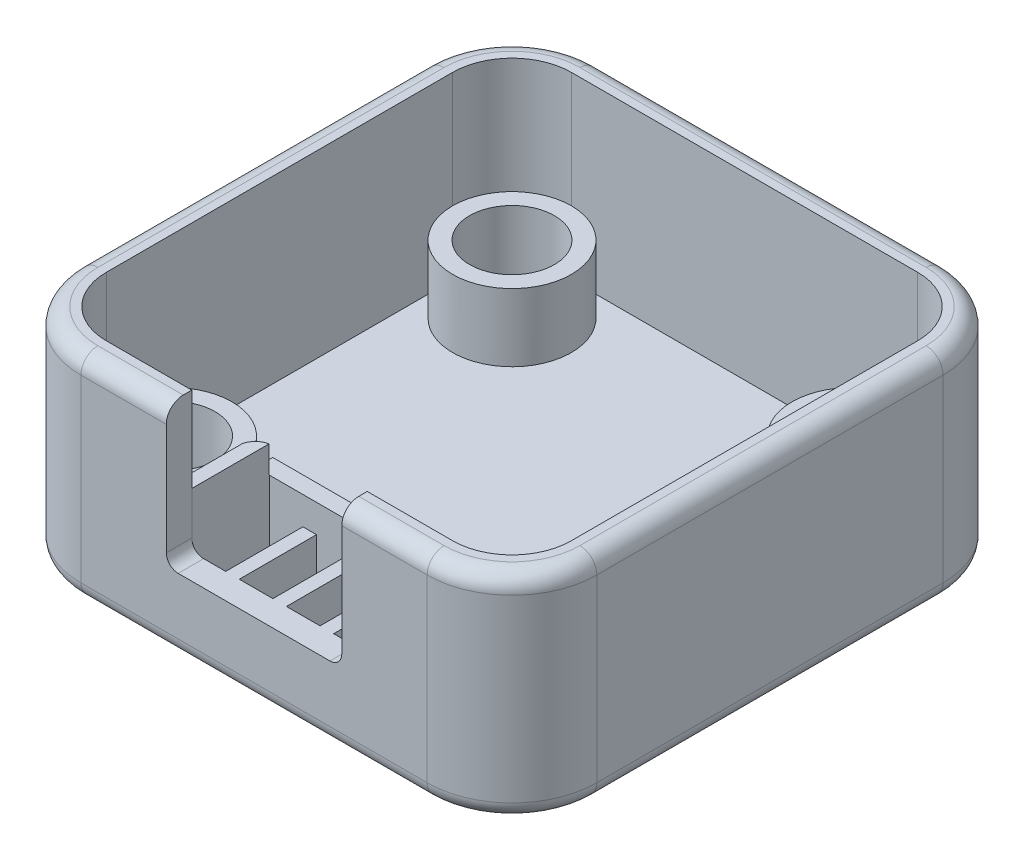
SolidWorks part; units mm, degrees
ref_plane "Front Plane" through (0, 0, 0) normal (0, 0, 1) x (1, 0, 0)
ref_plane "Top Plane" through (0, 0, 0) normal (0, 1, 0) x (1, 0, 0)
ref_plane "Right Plane" through (0, 0, 0) normal (1, 0, 0) x (0, 0, -1)
sketch "Sketch2" plane through (0, -1.6, 0) normal (0, -1, 0) x (1, 0, 0)
  line L1 (-13.5, -3.5) -> (-13.5, -23.5) construction
  line L2 (15.2, -28.7) -> (-15.2, -28.7)
  line L3 (15.2, -28.7) -> (15.2, 1.7)
  line L4 (15.2, 1.7) -> (-15.2, 1.7)
  line L5 (-15.2, -28.7) -> (-15.2, 1.7)
  line L6 (-6.77, 0) -> (-10, 0) construction
  line L7 (13.5, -23.5) -> (13.5, -3.5) construction
  line L8 (9, -27) -> (-9, -27) construction
  dimension "D1" = 1.7
  dimension "D2" = 1.7
  dimension "D3" = 1.7
  dimension "D4" = 1.7
extrude "Boss-Extrude1" add sketch "Sketch2" along normal blind 6
fillet "Fillet1" radius 5 4 edges at (15.2, -4.6, 1.7) (15.2, -4.6, -28.7) (-15.2, -4.6, 1.7) (-15.2, -4.6, -28.7)
fillet "Fillet2" radius 1 8 edges at (13.7355, -7.6, -27.2355) (15.2, -7.6, -13.5) (13.7355, -7.6, 0.2355) (0, -7.6, 1.7) (-13.7355, -7.6, 0.2355) (-15.2, -7.6, -13.5) (-13.7355, -7.6, -27.2355) (0, -7.6, -28.7)
sketch "Sketch3" plane through (0, -7.6, 0) normal (0, -1, 0) x (1, 0, 0)
  line L12 (10.2, -1.8) -> (-10.2, -1.8)
  line L13 (11.7, -23.7) -> (11.7, -3.3)
  line L14 (-10.2, -25.2) -> (10.2, -25.2)
  line L15 (-11.7, -3.3) -> (-11.7, -23.7)
  line L16 (10.2, -1.8) -> (-10.2, -1.8)
  line L17 (11.7, -23.7) -> (11.7, -3.3)
  line L18 (-10.2, -25.2) -> (10.2, -25.2)
  line L19 (-11.7, -3.3) -> (-11.7, -23.7)
  arc A12 (-10.2, -1.8) -> (-11.7, -3.3) centre (-10.2, -3.3) ccw
  arc A13 (11.7, -3.3) -> (10.2, -1.8) centre (10.2, -3.3) ccw
  arc A14 (10.2, -25.2) -> (11.7, -23.7) centre (10.2, -23.7) ccw
  arc A15 (-11.7, -23.7) -> (-10.2, -25.2) centre (-10.2, -23.7) ccw
  arc A16 (-10.2, -1.8) -> (-11.7, -3.3) centre (-10.2, -3.3) ccw
  arc A17 (11.7, -3.3) -> (10.2, -1.8) centre (10.2, -3.3) ccw
  arc A18 (10.2, -25.2) -> (11.7, -23.7) centre (10.2, -23.7) ccw
  arc A19 (-11.7, -23.7) -> (-10.2, -25.2) centre (-10.2, -23.7) ccw
  dimension "D1" = 3.5
extrude "Cut-Extrude1" cut sketch "Sketch3" against normal blind 0.5
sketch "Sketch4" plane through (0, -1.6, 0) normal (0, 1, 0) x (1, 0, 0)
  line L0 (15.2, 23.7) -> (15.2, 3.3) construction
  line L1 (-10.2, 28.7) -> (10.2, 28.7) construction
  line L2 (-15.2, 3.3) -> (-15.2, 23.7) construction
  line L3 (10.2, -1.7) -> (-10.2, -1.7) construction
  line L4 (15.2, 23.7) -> (15.2, 3.3)
  line L5 (-10.2, 28.7) -> (10.2, 28.7)
  line L6 (-15.2, 3.3) -> (-15.2, 23.7)
  line L7 (10.2, -1.7) -> (-10.2, -1.7)
  arc A0 (15.2, 23.7) -> (10.2, 28.7) centre (10.2, 23.7) ccw construction
  arc A1 (-10.2, 28.7) -> (-15.2, 23.7) centre (-10.2, 23.7) ccw construction
  arc A2 (-15.2, 3.3) -> (-10.2, -1.7) centre (-10.2, 3.3) ccw construction
  arc A3 (10.2, -1.7) -> (15.2, 3.3) centre (10.2, 3.3) ccw construction
  arc A4 (15.2, 23.7) -> (10.2, 28.7) centre (10.2, 23.7) ccw
  arc A5 (-10.2, 28.7) -> (-15.2, 23.7) centre (-10.2, 23.7) ccw
  arc A6 (-15.2, 3.3) -> (-10.2, -1.7) centre (-10.2, 3.3) ccw
  arc A7 (10.2, -1.7) -> (15.2, 3.3) centre (10.2, 3.3) ccw
extrude "Boss-Extrude2" add sketch "Sketch4" along normal blind 6.6
sketch "Sketch5" plane through (0, 5, 0) normal (0, 1, 0) x (1, 0, 0)
  line L8 (10.2, 27.2) -> (-10.2, 27.2)
  line L9 (-13.7, 23.7) -> (-13.7, 3.3)
  line L10 (-10.2, -0.2) -> (10.2, -0.2)
  line L11 (13.7, 3.3) -> (13.7, 23.7)
  line L12 (10.2, 27.2) -> (-10.2, 27.2)
  line L13 (-13.7, 23.7) -> (-13.7, 3.3)
  line L14 (-10.2, -0.2) -> (10.2, -0.2)
  line L15 (13.7, 3.3) -> (13.7, 23.7)
  arc A8 (13.7, 23.7) -> (10.2, 27.2) centre (10.2, 23.7) ccw
  arc A9 (-10.2, 27.2) -> (-13.7, 23.7) centre (-10.2, 23.7) ccw
  arc A10 (-13.7, 3.3) -> (-10.2, -0.2) centre (-10.2, 3.3) ccw
  arc A11 (10.2, -0.2) -> (13.7, 3.3) centre (10.2, 3.3) ccw
  arc A12 (13.7, 23.7) -> (10.2, 27.2) centre (10.2, 23.7) ccw
  arc A13 (-10.2, 27.2) -> (-13.7, 23.7) centre (-10.2, 23.7) ccw
  arc A14 (-13.7, 3.3) -> (-10.2, -0.2) centre (-10.2, 3.3) ccw
  arc A15 (10.2, -0.2) -> (13.7, 3.3) centre (10.2, 3.3) ccw
  dimension "D1" = 1.5
extrude "Cut-Extrude2" cut sketch "Sketch5" against normal offset from surface (10.6 mm away) 1.5 up to face at (0, -7.1, -13.5)
fillet "Fillet3" radius 1 8 edges at (13.7355, 5, -27.2355) (0, 5, -28.7) (-13.7355, 5, -27.2355) (-15.2, 5, -13.5) (-13.7355, 5, 0.2355) (0, 5, 1.7) (13.7355, 5, 0.2355) (15.2, 5, -13.5)
sketch "Sketch6" plane through (0, 0, 1.7) normal (0, 0, 1) x (1, 0, 0)
  line L0 (5.17, -2.55) -> (5.17, 0.95) construction
  line L2 (-5.17, 0.95) -> (-5.17, -2.55) construction
  line L3 (-4.47, -3.25) -> (4.47, -3.25) construction
  line L4 (5.17, -2.55) -> (5.17, 5)
  line L6 (-5.17, 5) -> (-5.17, -2.55)
  line L7 (-4.47, -3.25) -> (4.47, -3.25)
  line L8 (-10.2, 5) -> (10.2, 5) construction
  line L9 (-5.17, 5) -> (5.17, 5)
  arc A0 (4.47, -3.25) -> (5.17, -2.55) centre (4.47, -2.55) ccw construction
  arc A3 (-5.17, -2.55) -> (-4.47, -3.25) centre (-4.47, -2.55) ccw construction
  arc A4 (4.47, -3.25) -> (5.17, -2.55) centre (4.47, -2.55) ccw
  arc A7 (-5.17, -2.55) -> (-4.47, -3.25) centre (-4.47, -2.55) ccw
extrude "Cut-Extrude3" cut sketch "Sketch6" against normal up to next
sketch "Sketch9" plane through (0, -5.6, 0) normal (0, 1, 0) x (1, 0, 0)
  line L0 (5.97, 3.35) -> (5.97, 0) construction
  line L1 (5.17, 4.35) -> (5.17, 0) construction
  line L2 (5.97, 5.35) -> (5.97, -0.2)
  line L3 (5.17, 5.35) -> (5.17, -0.2)
  line L5 (5.97, -0.2) -> (5.17, -0.2)
  line L6 (5.17, 5.35) -> (5.97, 5.35)
  line L7 (5.17, -0.2) -> (10.2, -0.2) construction
  point P11 (5.57, -0.2)
extrude "Boss-Extrude5" add sketch "Sketch9" along normal up to vertex (2.35 mm away)
pattern_linear "LPattern1" count 5 spacing 2.78 along (-1, 0, 0) of "Boss-Extrude5"
sketch "Sketch10" plane through (0, 0, -5.35) normal (0, 0, -1) x (-1, 0, 0)
  line L0 (5.95, -3.25) -> (5.95, -5.6) construction
  line L1 (-5.97, -3.25) -> (-5.97, -5.6) construction
  line L2 (5.95, -3.25) -> (5.95, -5.6)
  line L3 (-5.97, -3.25) -> (-5.97, -5.6)
  line L4 (-5.97, -5.6) -> (5.95, -5.6)
  line L5 (5.95, -3.25) -> (-5.97, -3.25)
extrude "Boss-Extrude6" add sketch "Sketch10" against normal blind 1
sketch "Sketch11" plane through (0, -3.25, 0) normal (0, 1, 0) x (1, 0, 0)
  line L0 (3.19, 4.35) -> (5.17, 4.35) construction
  line L1 (5.17, -0.2) -> (5.97, -0.2) construction
  line L2 (5.17, 4.35) -> (5.17, -0.2) construction
  line L3 (-5.15, -0.2) -> (-5.15, 4.35) construction
  line L4 (-5.95, -0.2) -> (-5.15, -0.2) construction
  line L5 (-5.95, 5.35) -> (-5.95, -0.2) construction
  line L6 (5.97, 5.35) -> (-5.95, 5.35) construction
  line L7 (5.97, -0.2) -> (5.97, 5.35) construction
  line L8 (-5.15, 4.35) -> (5.17, 4.35)
  line L9 (5.17, -0.2) -> (5.97, -0.2)
  line L10 (5.17, 4.35) -> (5.17, -0.2)
  line L11 (-5.15, -0.2) -> (-5.15, 4.35)
  line L12 (-5.95, -0.2) -> (-5.15, -0.2)
  line L13 (-5.95, 5.35) -> (-5.95, -0.2)
  line L14 (5.97, 5.35) -> (-5.95, 5.35)
  line L15 (5.97, -0.2) -> (5.97, 5.35)
extrude "Boss-Extrude7" add sketch "Sketch11" along normal up to vertex (1.65 mm away)
sketch "Sketch12" plane through (0, -5.6, 0) normal (0, 1, 0) x (1, 0, 0)
  circle A0 centre (10, 3.5) radius 3.5
  circle A1 centre (10, 23.5) radius 3.5
  circle A2 centre (-10, 23.5) radius 3.5
  circle A3 centre (-10, 3.5) radius 3.5
  circle A4 centre (10, 23.5) radius 2.5
  circle A5 centre (-10, 23.5) radius 2.5
  circle A6 centre (10, 3.5) radius 2.5
  circle A7 centre (-10, 3.5) radius 2.5
  dimension "D1" = 7
  dimension "D2" = 5
extrude "Boss-Extrude8" add sketch "Sketch12" along normal up to vertex (3.99 mm away)
sketch "Sketch13" plane through (0, -1.6, 0) normal (0, 1, 0) x (1, 0, 0)
  line L0 (-5.95, -0.2) -> (-5.17, -0.2) construction
  line L1 (-5.15, -0.2) -> (-5.15, 4.35) construction
  line L2 (-5.95, 5.35) -> (-5.95, -0.2) construction
  line L3 (-5.95, -0.2) -> (-5.15, -0.2)
  line L4 (-5.15, -0.2) -> (-5.15, 4.3337)
  line L5 (-5.95, 3.549) -> (-5.95, -0.2)
  line L6 (5.17, -0.2) -> (5.97, -0.2) construction
  line L7 (5.17, 4.35) -> (5.17, -0.2) construction
  line L8 (5.97, -0.2) -> (5.97, 5.35) construction
  line L9 (5.17, -0.2) -> (5.97, -0.2)
  line L10 (5.17, 4.3298) -> (5.17, -0.2)
  line L11 (5.97, -0.2) -> (5.97, 3.35)
  arc A0 (-4.97, 4.35) -> (-5.97, 3.35) centre (-4.97, 3.35) ccw construction
  arc A1 (-5.15, 4.3337) -> (-5.95, 3.549) centre (-4.97, 3.35) ccw
  arc A2 (5.97, 3.35) -> (4.97, 4.35) centre (4.97, 3.35) ccw construction
  arc A3 (5.97, 3.35) -> (5.17, 4.3298) centre (4.97, 3.35) ccw
extrude "Boss-Extrude9" add sketch "Sketch13" along normal up to vertex (1.6 mm away)
equation "\"f\"= 0.0017"
equation "\"D3@Sketch2\"=\"f\""
equation "\"D2@Sketch2\"=\"f\""
equation "\"D1@Sketch2\"=\"f\""
equation "\"D4@Sketch2\"=\"f\""
equation "\"g\"=0.007"
equation "\"D1@Sketch12\"=\"g\""
equation "\"h\"=0.005"
equation "\"D2@Sketch12\"=\"h\""
